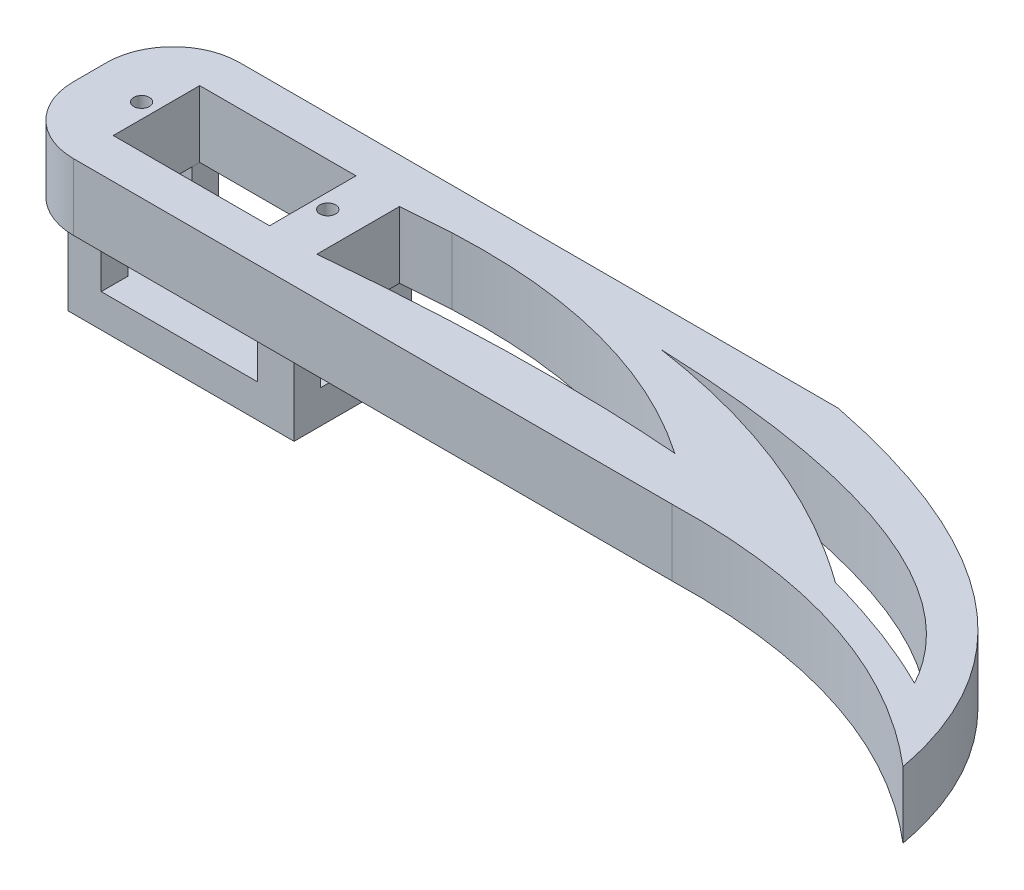
SolidWorks part; units mm, degrees
ref_plane "Front Plane" through (0, 0, 0) normal (0, 0, 1) x (1, 0, 0)
ref_plane "Top Plane" through (0, 0, 0) normal (0, 1, 0) x (1, 0, 0)
ref_plane "Right Plane" through (0, 0, 0) normal (1, 0, 0) x (0, 0, -1)
sketch "Sketch1" plane through (0, 0, 0) normal (0, 1, 0) x (1, 0, 0)
  line L1 (0, 0) -> (100, 0)
  line L2 (0, 0) -> (0, 25)
  line L3 (0, 25) -> (100, 25)
  line L4 (100, 0) -> (100, 25)
  dimension "D1" = 25
  dimension "D2" = 100
extrude "Boss-Extrude1" add sketch "Sketch1" along normal blind 10
sketch "Sketch2" plane through (0, 10, 0) normal (0, 1, 0) x (1, 0, 0)
  line L0 (0, 12.5) -> (100, 12.5) construction
  line L1 (10, 19) -> (33.5, 19)
  line L2 (10, 19) -> (10, 6)
  line L3 (10, 6) -> (33.5, 6)
  line L4 (33.5, 19) -> (33.5, 6)
  line L5 (0, 25) -> (0, 0) construction
  line L6 (100, 0) -> (100, 25) construction
  line L7 (21.75, 19) -> (21.75, 6) construction
  circle A0 centre (7.75, 12.5) radius 1.19
  circle A1 centre (35.75, 12.5) radius 1.19
  point P16 (21.75, 12.5)
  dimension "D5" = 14
  dimension "D6" = 14
  dimension "D7" = 2.38
  dimension "D8" = 2.38
  dimension "D1" = 23.5
  dimension "D2" = 13
  dimension "D3" = 6.5
  dimension "D4" = 10
extrude "Cut-Extrude1" cut sketch "Sketch2" against normal blind 10
sketch "Sketch3" plane through (0, 10, 0) normal (0, 1, 0) x (1, 0, 0)
  line L0 (100, 25) -> (100, 0)
  line L4 (0, 25) -> (0, 0)
  line L5 (0, 0) -> (100, 0)
  line L6 (100, 0) -> (100, 25)
  line L7 (100, 25) -> (0, 25)
  line L8 (0, 25) -> (0, 0)
  line L9 (0, 0) -> (100, 0)
  line L11 (100, 25) -> (0, 25)
  spline S0 degree 2 poles (100, 25) (145.5833, 15.8484) (151.536, -16.7875) knots 0 0 0 1 1 1
  spline S1 degree 2 poles (100, 0) (130.9105, 0.7919) (151.536, -16.7875) knots 0 0 0 1 1 1
  line M13 (100, 0) -> (100, 25)
  dimension "D1" = 0
extrude "Boss-Extrude2" add sketch "Sketch3" against normal blind 10 contours S1 S0 M13
fillet "Fillet1" radius 10 2 edges at (0, 5, -25) (0, 5, 0)
sketch "Sketch7" plane through (0, 0, 0) normal (0, -1, 0) x (1, 0, 0)
  line L1 (4.9234, -4.2648) -> (38.9234, -4.2648)
  line L2 (4.9234, -4.2648) -> (4.9234, -21.9231)
  line L3 (4.9234, -21.9231) -> (38.9234, -21.9231)
  line L4 (38.9234, -4.2648) -> (38.9234, -21.9231)
  dimension "D1" = 34
extrude "Boss-Extrude3" add sketch "Sketch7" along normal blind 14.5
sketch "Sketch8" plane through (0, 0, -4.2648) normal (0, 0, 1) x (1, 0, 0)
  line L5 (38.9234, 0) -> (4.9234, 0) construction
  line L6 (9.9234, 0) -> (33.4234, 0)
  line L7 (9.9234, 0) -> (9.9234, -9.5)
  line L8 (9.9234, -9.5) -> (33.4234, -9.5)
  line L9 (33.4234, 0) -> (33.4234, -9.5)
  line L10 (4.9234, -14.5) -> (4.9234, 0) construction
  line L13 (38.9234, -14.5) -> (4.9234, -14.5) construction
  dimension "D1" = 5
  dimension "D2" = 23.5
  dimension "D3" = 5
extrude "Cut-Extrude2" cut sketch "Sketch8" against normal through all
sketch "Sketch9" plane through (4.9234, 0, 0) normal (-1, 0, 0) x (0, 0, 1)
  line L0 (-4.2648, 0) -> (-21.9231, 0) construction
  line L1 (-17.9231, 0) -> (-8.2648, 0)
  line L2 (-17.9231, 0) -> (-17.9231, -9.5)
  line L3 (-17.9231, -9.5) -> (-8.2648, -9.5)
  line L4 (-8.2648, 0) -> (-8.2648, -9.5)
  line L5 (-21.9231, -14.5) -> (-21.9231, 0) construction
  line L6 (-4.2648, -14.5) -> (-4.2648, 0) construction
  line L7 (-4.2648, -14.5) -> (-21.9231, -14.5) construction
  dimension "D1" = 4
  dimension "D2" = 4
  dimension "D3" = 5
extrude "Cut-Extrude3" cut sketch "Sketch9" against normal through all
sketch "Sketch10" plane through (0, -14.5, 0) normal (0, -1, 0) x (1, 0, 0)
  line L0 (0, -12.5) -> (40.5304, -12.5) construction
  line L3 (0, -15) -> (0, -10) construction
  circle A0 centre (16.5, -12.5) radius 2.8991
  circle A1 centre (7.75, -12.5) radius 1.19 construction
  dimension "D1" = 8.75
extrude "Boss-Extrude4" add sketch "Sketch10" along normal blind 5
sketch "Sketch13" plane through (0, 10, 0) normal (0, 1, 0) x (1, 0, 0)
  line L1 (40.7591, 18.2805) -> (125.2534, 24.9895) construction
  line L2 (125.2534, 24.9895) -> (141.5631, -5.0876) construction
  line L3 (40.7591, 13.9584) -> (40.7591, 5.8509)
  line L5 (40.7591, 5.8509) -> (79.6786, 9.5511) construction
  line L6 (79.6786, 9.5511) -> (107.4894, 5.2143) construction
  line L7 (128.0897, 0.4171) -> (135.3664, -1.9446) construction
  line L8 (135.3664, -1.9446) -> (141.5631, -5.0876) construction
  line L9 (40.7591, 18.2805) -> (40.7591, 13.9584)
  spline S0 degree 2 poles (40.7591, 18.2805) (125.2534, 24.9895) (141.5631, -5.0876) knots 0 0 0 1 1 1
  spline S1 degree 2 poles (40.7591, 5.8509) (79.6786, 9.5511) (107.4894, 5.2143) knots 0 0 0 1 1 1
  spline S3 degree 2 poles (79.0598, 19.324) (103.5733, 15.7547) (122.4877, 2.0984) knots 0 0 0 0.958851 0.958851 0.958851
  spline S4 degree 2 poles (128.0897, 0.4171) (135.3664, -1.9446) (141.5631, -5.0876) knots 0 0 0 1 1 1
  spline S5 degree 2 poles (107.4894, 5.2143) (119.5492, 3.4815) (130.9501, -0.5563) knots 0 0 0 1 1 1
  spline S6 degree 2 poles (48.109, 18.8026) (74.2926, 20.0653) (93.6269, 6.823) knots 0 0 0 0.932257 0.932257 0.932257
  spline S7 degree 2 poles (100.7037, 6.2724) (100.9827, 6.1703) (101.2618, 6.0681) knots 0.984752 0.984752 0.984752 1 1 1
extrude "Cut-Extrude4" cut sketch "Sketch13" against normal through all
